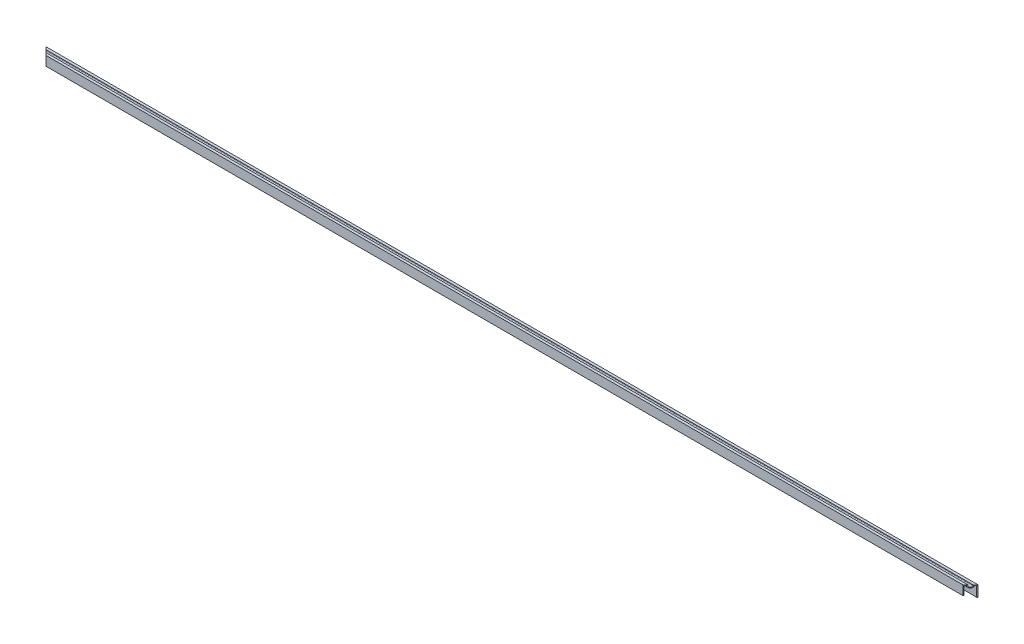
SolidWorks part; units mm, degrees
material "6063-O"
ref_plane "Front Plane" through (0, 0, 0) normal (0, 0, 1) x (1, 0, 0)
ref_plane "Top Plane" through (0, 0, 0) normal (0, 1, 0) x (1, 0, 0)
ref_plane "Right Plane" through (0, 0, 0) normal (1, 0, 0) x (0, 0, -1)
sketch "Sketch1" plane through (0, 0, 0) normal (1, 0, 0) x (0, 0, -1)
  line L0 (0, 0) -> (0, 21.844)
  line L1 (0, 21.844) -> (-5.08, 21.844)
  line L2 (-5.08, 21.844) -> (-5.08, 20.066)
  line L3 (-10.16, 20.066) -> (-10.16, 21.844)
  line L4 (-10.16, 21.844) -> (-15.24, 21.844)
  line L5 (-15.24, 21.844) -> (-15.24, 3.048)
  line L6 (-1.27, 0) -> (-1.27, 20.574)
  line L7 (-1.27, 20.574) -> (-3.81, 20.574)
  line L8 (-3.81, 20.574) -> (-3.81, 20.066)
  line L9 (-11.43, 20.066) -> (-11.43, 20.574)
  line L10 (-11.43, 20.574) -> (-13.97, 20.574)
  line L11 (-13.97, 20.574) -> (-13.97, 3.048)
  line L12 (0, 0) -> (-1.27, 0)
  line L13 (-15.24, 3.048) -> (-13.97, 3.048)
  arc A0 (-5.08, 20.066) -> (-10.16, 20.066) centre (-7.62, 20.066) cw
  arc A1 (-3.81, 20.066) -> (-11.43, 20.066) centre (-7.62, 20.066) cw
  dimension "D1" = 4.318
  dimension "D2" = 21.844
  dimension "D3" = 18.796
  dimension "D4" = 15.24
  dimension "D5" = 5.08
  dimension "D6" = 12.7
extrude "Boss-Extrude1" add sketch "Sketch1" along normal mid plane 1868.4875
sketch "Sketch3" [suppressed] plane through (0, 21.844, 0) normal (0, 1, 0) x (1, 0, 0)
  line L0 (407.4462, 0) -> (392.2062, 0)
  line L2 (392.2062, 0) -> (407.4462, -15.24)
  line L3 (407.4462, -15.24) -> (407.4462, 0)
  line L4 (407.4462, 0) -> (-407.4462, 0) construction
extrude "Cut-Top-Right-Back" [suppressed] cut sketch "Sketch3" against normal through all
sketch "Sketch5" [suppressed] plane through (0, 21.844, 0) normal (0, 1, 0) x (1, 0, 0)
  line L0 (-407.4462, 0) -> (-392.2062, 0)
  line L2 (-392.2062, 0) -> (-407.4462, -15.24)
  line L3 (-407.4462, -15.24) -> (-407.4462, 0)
  line L4 (407.4462, 0) -> (-407.4462, 0) construction
extrude "Cut-Top-Left-Back" [suppressed] cut sketch "Sketch5" against normal through all
sketch "Sketch8" [suppressed] plane through (0, 0, 15.24) normal (0, 0, 1) x (1, 0, 0)
  line L0 (407.4462, 0) -> (385.6022, 21.844)
  line L1 (407.4462, 21.844) -> (-407.4462, 21.844) construction
  line L2 (385.6022, 21.844) -> (407.4462, 21.844)
  line L3 (407.4462, 21.844) -> (407.4462, 0)
extrude "Cut-Front-Right-Top" [suppressed] cut sketch "Sketch8" against normal through all
sketch "Sketch6" [suppressed] plane through (0, 0, 15.24) normal (0, 0, 1) x (1, 0, 0)
  line L0 (-407.4462, 0) -> (-385.6022, 21.844)
  line L1 (407.4462, 21.844) -> (-407.4462, 21.844) construction
  line L2 (-385.6022, 21.844) -> (-407.4462, 21.844)
  line L3 (-407.4462, 21.844) -> (-407.4462, 0)
extrude "Cut-Front-Left-Top" [suppressed] cut sketch "Sketch6" against normal through all
sketch "Sketch7" [suppressed] plane through (0, 0, 15.24) normal (0, 0, 1) x (1, 0, 0)
  line L0 (-407.4462, 21.844) -> (-385.6022, 0)
  line L1 (407.4462, 0) -> (-407.4462, 0) construction
  line L2 (-385.6022, 0) -> (-407.4462, 0)
  line L3 (-407.4462, 0) -> (-407.4462, 21.844)
extrude "Cut-Front-Left-Bottom" [suppressed] cut sketch "Sketch7" against normal through all
sketch "Sketch2" plane through (0, 21.844, 0) normal (0, 1, 0) x (1, 0, 0)
  line L0 (934.2437, 0) -> (919.0037, -15.24)
  line L1 (934.2437, -15.24) -> (-934.2437, -15.24) construction
  line L2 (919.0037, -15.24) -> (934.2437, -15.24)
  line L3 (934.2437, -15.24) -> (934.2437, 0)
extrude "Cut-Top-Right-Front" cut sketch "Sketch2" against normal through all
sketch "Sketch4" plane through (0, 21.844, 0) normal (0, 1, 0) x (1, 0, 0)
  line L0 (-934.2437, 0) -> (-919.0037, -15.24)
  line L1 (919.0037, -15.24) -> (-934.2437, -15.24) construction
  line L2 (-919.0037, -15.24) -> (-934.2437, -15.24)
  line L3 (-934.2437, -15.24) -> (-934.2437, 0)
extrude "Cut-Top-Left-Front" cut sketch "Sketch4" against normal through all
sketch "Sketch9" [suppressed] plane through (0, 0, 15.24) normal (0, 0, 1) x (1, 0, 0)
  line L0 (407.4462, 21.844) -> (385.6022, 0)
  line L1 (407.4462, 0) -> (-406.1762, 0) construction
  line L2 (385.6022, 0) -> (407.4462, 0)
  line L3 (407.4462, 0) -> (407.4462, 21.844)
extrude "Cut-Front-Right-Bottom" [suppressed] cut sketch "Sketch9" against normal through all
